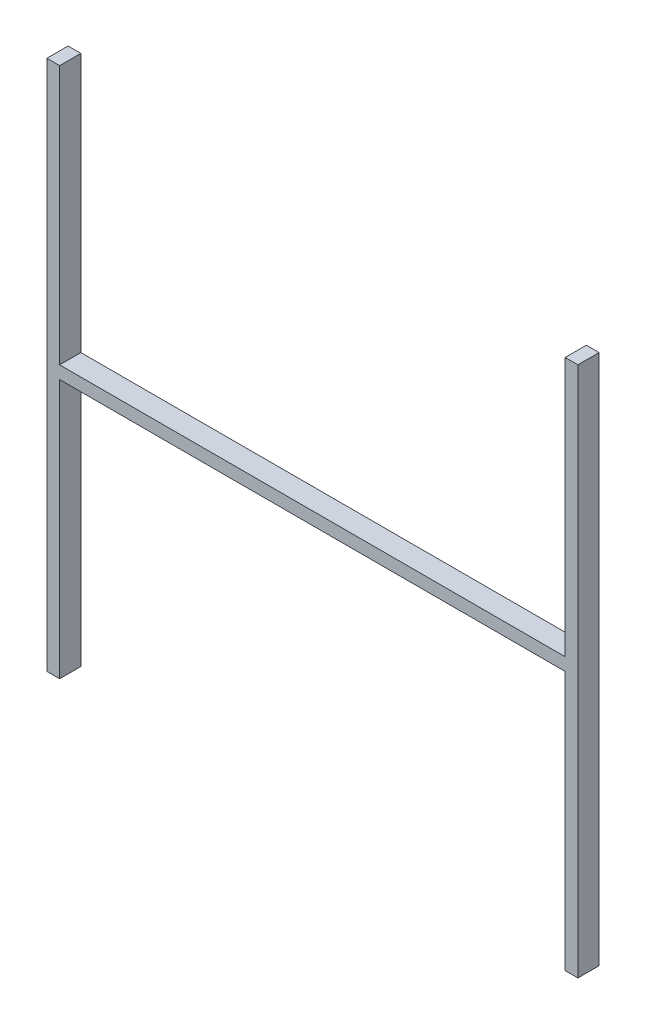
SolidWorks part; units mm, degrees
ref_plane "Plano frontal" through (0, 0, 0) normal (0, 0, 1) x (1, 0, 0)
ref_plane "Plano superior" through (0, 0, 0) normal (0, 1, 0) x (1, 0, 0)
ref_plane "Plano direito" through (0, 0, 0) normal (1, 0, 0) x (0, 0, -1)
sketch "Esboço1" plane through (0, 0, 0) normal (0, 0, 1) x (1, 0, 0)
  line L0 (-122, 125) -> (-122, -125) construction
  line L1 (-122, 0) -> (122, 0) construction
  line L2 (0, 0) -> (0, 61.9263) construction
  line L3 (122, 125) -> (122, -125) construction
  line L4 (-125, 125) -> (-125, -125)
  line L5 (-119, -3) -> (119, -3)
  line L6 (119, 125) -> (119, 3)
  line L7 (-119, 125) -> (-119, 3)
  line L8 (-119, 3) -> (119, 3)
  line L9 (125, 125) -> (125, -125)
  line L10 (-125, 125) -> (-119, 125)
  line L11 (-125, -125) -> (-119, -125)
  line L12 (-119, -3) -> (-119, -125)
  line L14 (119, 125) -> (125, 125)
  line L15 (119, -125) -> (125, -125)
  line L16 (-122, 3) -> (122, 3) construction
  line L17 (-122, -3) -> (122, -3) construction
  line L18 (-119, 125) -> (-119, -125) construction
  line L19 (119, -3) -> (119, -125)
  line L20 (119, 125) -> (119, -125) construction
  dimension "D3" = 250
  dimension "D4" = 250
  dimension "D1" = 3
  dimension "D2" = 3
extrude "Ressalto-extrusão1" add sketch "Esboço1" along normal blind 10
